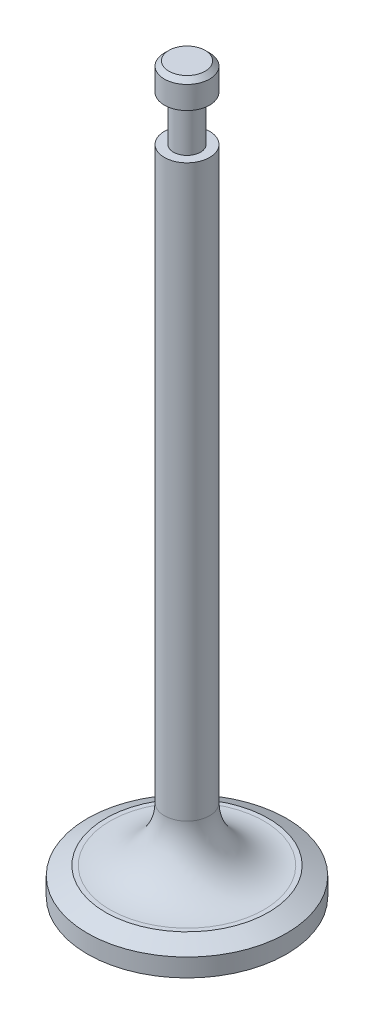
SolidWorks part; units mm, degrees
ref_plane "Front Plane" through (0, 0, 0) normal (0, 0, 1) x (1, 0, 0)
ref_plane "Top Plane" through (0, 0, 0) normal (0, 1, 0) x (1, 0, 0)
ref_plane "Right Plane" through (0, 0, 0) normal (1, 0, 0) x (0, 0, -1)
sketch "Sketch1" plane through (0, 0, 0) normal (0, 0, 1) x (1, 0, 0)
  line L0 (0, 0) -> (0, 80)
  line L1 (0, 80) -> (2.5, 80)
  line L2 (2.5, 80) -> (2.5, 77)
  line L3 (2.5, 77) -> (1.5, 77)
  line L4 (1.5, 77) -> (1.5, 72)
  line L5 (1.5, 72) -> (2.5, 72)
  line L6 (2.5, 72) -> (2.5, 3)
  line L7 (2.5, 3) -> (11, 3)
  line L8 (11, 3) -> (11, 0)
  line L9 (11, 0) -> (0, 0)
  dimension "D1" = 1
  dimension "D2" = 80
  dimension "D3" = 3
  dimension "D4" = 11
  dimension "D5" = 3
  dimension "D6" = 2.5
  dimension "D7" = 5
revolve "Revolve1" add sketch "Sketch1" angle 360 about L0
fillet "Fillet1" radius 6 1 edges at (0, 3, -2.5)
chamfer "Chamfer1" distance 0.5 angle 45 1 edges at (0, 80, -2.5)
chamfer "Chamfer2" distance 2 distance2 1 1 edges at (0, 3, -11)
